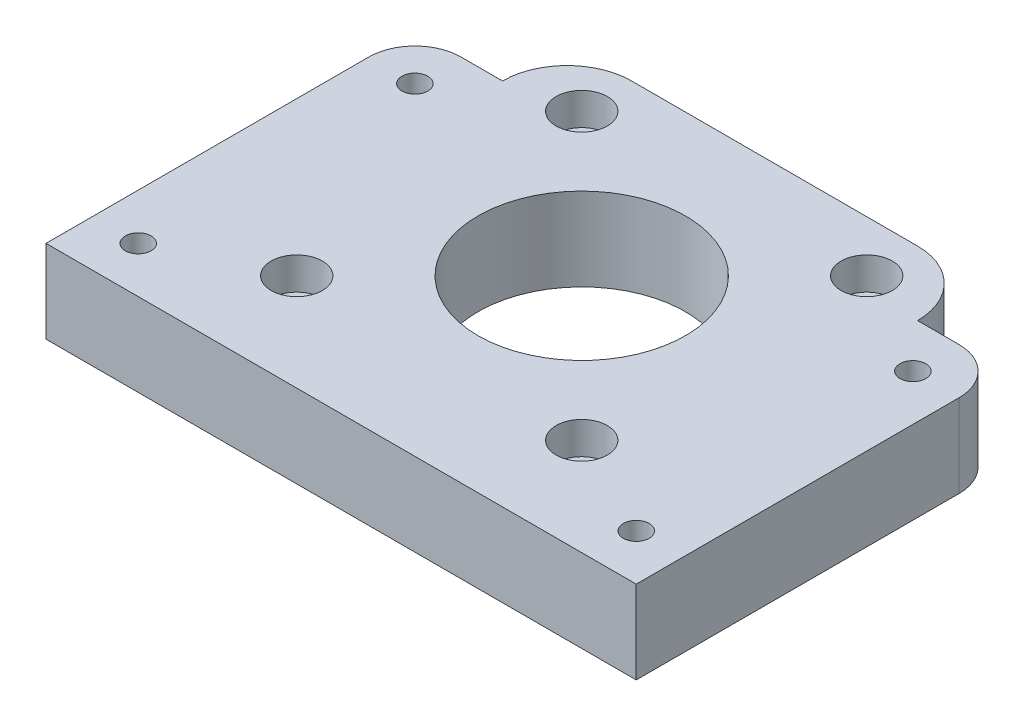
SolidWorks part; units mm, degrees
ref_plane "Front Plane" through (0, 0, 0) normal (0, 0, 1) x (1, 0, 0)
ref_plane "Top Plane" through (0, 0, 0) normal (0, 1, 0) x (1, 0, 0)
ref_plane "Right Plane" through (0, 0, 0) normal (1, 0, 0) x (0, 0, -1)
sketch "Sketch1" plane through (0, 0, 0) normal (0, 1, 0) x (1, 0, 0)
  line L1 (-15.5, 29.5) -> (15.5, 29.5)
  line L5 (-32, 0) -> (32, 0) construction
  line L6 (0, 29.5) -> (0, -17.5) construction
  line L7 (-32, -17.5) -> (-32, 17.5)
  line L8 (-27, 22.5) -> (-22.5, 22.5)
  line L10 (32, -17.5) -> (32, 17.5)
  line L11 (27, 22.5) -> (22.5, 22.5)
  line L12 (-32, -17.5) -> (32, -17.5)
  line L13 (-15.5, 29.5) -> (-15.5, 22.5) construction
  line L14 (-15.5, 22.5) -> (-22.5, 22.5) construction
  line L15 (15.5, 22.5) -> (15.5, 29.5) construction
  line L16 (15.5, 22.5) -> (22.5, 22.5) construction
  line L17 (-32, 17.5) -> (-27, 17.5) construction
  line L18 (-27, 22.5) -> (-27, 17.5) construction
  line L19 (27, 22.5) -> (27, 17.5) construction
  line L20 (32, 17.5) -> (27, 17.5) construction
  arc A0 (32, 17.5) -> (27, 22.5) centre (27, 17.5) ccw
  arc A1 (-32, 17.5) -> (-27, 22.5) centre (-27, 17.5) cw
  arc A2 (15.5, 29.5) -> (22.5, 22.5) centre (15.5, 22.5) cw
  arc A3 (-15.5, 29.5) -> (-22.5, 22.5) centre (-15.5, 22.5) ccw
  point P0 (0, 0)
  point P17 (0, 0)
  dimension "D5" = 31
  dimension "D1" = 7
  dimension "D2" = 5
  dimension "D3" = 64
  dimension "D4" = 47
extrude "Boss-Extrude1" add sketch "Sketch1" along normal blind 9
sketch "Sketch2" plane through (0, 9, 0) normal (0, 1, 0) x (1, 0, 0)
  line L0 (15.5, 29.5) -> (-15.5, 29.5) construction
  line L2 (32, -17.5) -> (32, 17.5) construction
  circle A0 centre (0.09, 8.5) radius 11.25
  dimension "D2" = 22.5
  dimension "D1" = 21
  dimension "D3" = 31.91
extrude "Cut-Extrude1" cut sketch "Sketch2" against normal blind 9 contours A0
sketch "Sketch3" plane through (0, 9, 0) normal (0, 1, 0) x (1, 0, 0)
  line L0 (-15.3603, 23.9503) -> (0.09, 8.5) construction
  line L1 (0.09, 8.5) -> (15.5403, 23.9503) construction
  line L2 (0.09, 8.5) -> (-15.3603, -6.9503) construction
  line L3 (0.09, 8.5) -> (15.5403, -6.9503) construction
  line L4 (-15.3603, 23.9503) -> (15.5403, 23.9503) construction
  line L5 (15.5403, 23.9503) -> (15.5403, -6.9503) construction
  line L6 (-15.3603, 23.9503) -> (-15.3603, -6.9503) construction
  line L7 (-15.3603, -6.9503) -> (15.5403, -6.9503) construction
  circle A0 centre (-15.3603, 23.9503) radius 2.775
  circle A1 centre (15.5403, 23.9503) radius 2.775
  circle A2 centre (15.5403, -6.9503) radius 2.775
  circle A3 centre (-15.3603, -6.9503) radius 2.775
  dimension "D1" = 5.55
  dimension "D2" = 21.85
extrude "Cut-Extrude2" cut sketch "Sketch3" against normal blind 3.5
sketch "Sketch5" plane through (0, 0, 0) normal (0, 1, 0) x (1, 0, 0)
  line L0 (-27, -12.5) -> (-32, -12.5) construction
  line L1 (-32, 17.5) -> (-32, -17.5) construction
  line L2 (-27, -12.5) -> (-27, -17.5) construction
  line L3 (-32, -17.5) -> (32, -17.5) construction
  line L4 (-32, 17.5) -> (-27, 17.5) construction
  line L5 (-27, 17.5) -> (-27, 22.5) construction
  line L6 (27, -17.5) -> (27, -12.5) construction
  line L7 (27, -12.5) -> (32, -12.5) construction
  line L8 (32, -17.5) -> (32, 17.5) construction
  line L9 (27, 22.5) -> (27, 17.5) construction
  line L11 (27, 17.5) -> (32, 17.5) construction
  line L12 (-22.5, 22.5) -> (-27, 22.5) construction
  line L13 (27, 22.5) -> (22.5, 22.5) construction
  circle A0 centre (-27, 17.5) radius 2.775
  circle A1 centre (27, 17.5) radius 2.775
  circle A2 centre (27, -12.5) radius 2.775
  circle A3 centre (-27, -12.5) radius 2.775
  dimension "D2" = 5.55
  dimension "D1" = 5
extrude "Cut-Extrude4" cut sketch "Sketch5" along normal blind 3.5
sketch "Sketch4" plane through (0, 5.5, 0) normal (0, 1, 0) x (1, 0, 0)
  circle A0 centre (-15.3603, 23.9503) radius 1.5
  circle A1 centre (15.5403, 23.9503) radius 1.5
  circle A2 centre (15.5403, -6.9503) radius 1.5
  circle A3 centre (-15.3603, -6.9503) radius 1.5
  dimension "D1" = 3
extrude "Cut-Extrude3" cut sketch "Sketch4" against normal blind 6
sketch "Sketch6" plane through (0, 3.5, 0) normal (0, -1, 0) x (-1, 0, 0)
  circle A0 centre (-27, -12.5) radius 1.4
  circle A1 centre (-27, 17.5) radius 1.4
  circle A2 centre (27, 17.5) radius 1.4
  circle A3 centre (27, -12.5) radius 1.4
  dimension "D1" = 2.8
extrude "Cut-Extrude5" cut sketch "Sketch6" against normal blind 6
